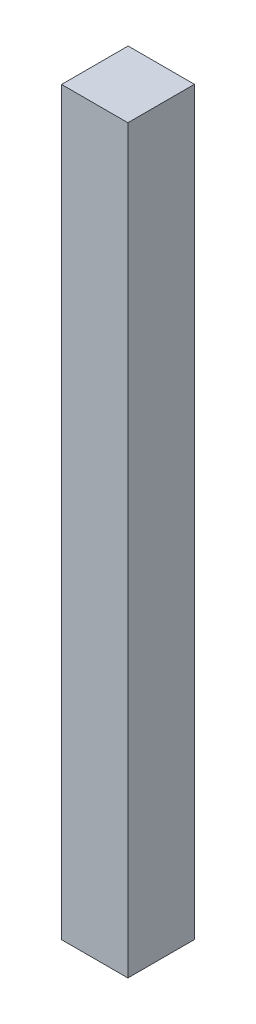
SolidWorks part; units mm, degrees
material "Cedar"
ref_plane "Front" through (0, 0, 0) normal (0, 0, 1) x (1, 0, 0)
ref_plane "Top" through (0, 0, 0) normal (0, 1, 0) x (1, 0, 0)
ref_plane "Right" through (0, 0, 0) normal (1, 0, 0) x (0, 0, -1)
sketch "Sketch1" plane through (0, 0, 0) normal (0, 1, 0) x (1, 0, 0)
  line L1 (-17.399, -17.4625) -> (17.399, -17.4625)
  line L2 (-17.399, -17.4625) -> (-17.399, 17.4625)
  line L3 (-17.399, 17.4625) -> (17.399, 17.4625)
  line L4 (17.399, -17.4625) -> (17.399, 17.4625)
  line L5 (-17.399, -17.4625) -> (17.399, 17.4625) construction
  line L6 (-17.399, 17.4625) -> (17.399, -17.4625) construction
  point P0 (0, 0)
  dimension "D1" = 34.925
  dimension "D2" = 34.798
extrude "Boss-Extrude1" add sketch "Sketch1" along normal blind 388.62 contours L1 L4 L3 L2
